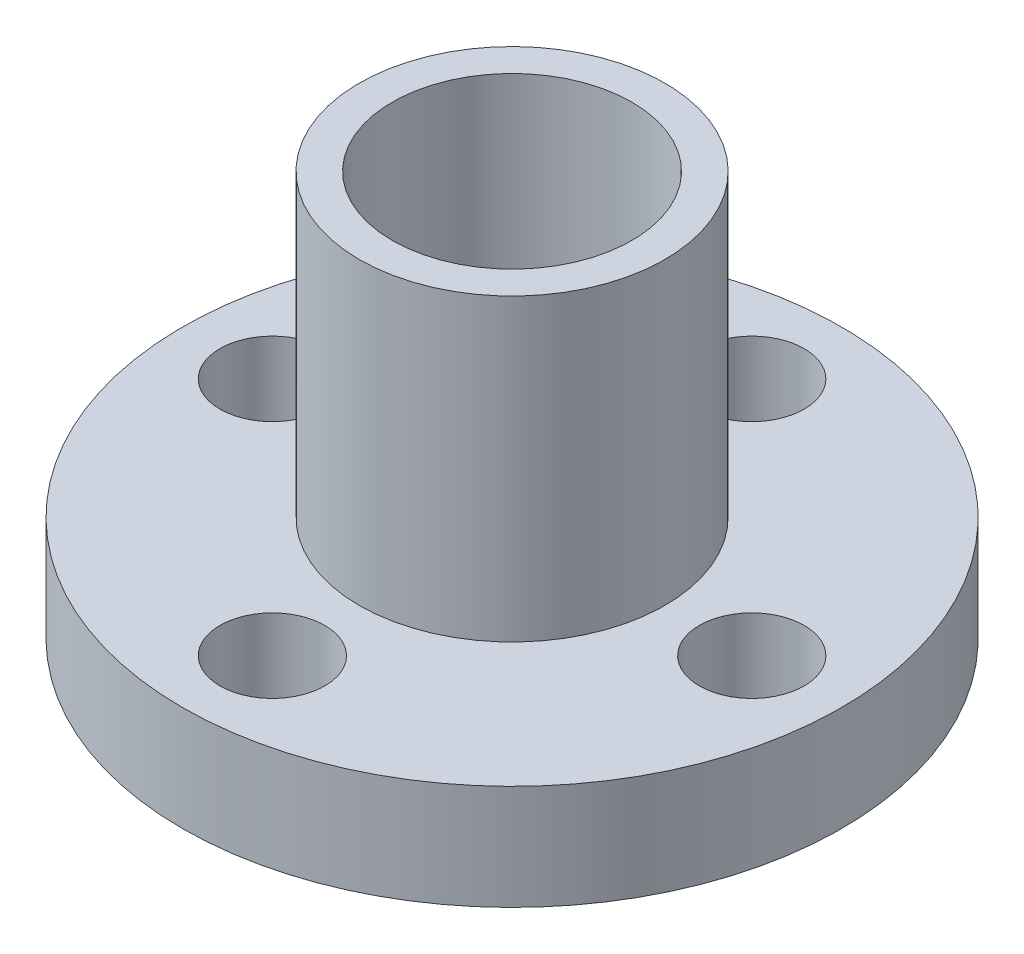
SolidWorks part; units mm, degrees
ref_plane "前视基准面" through (0, 0, 0) normal (0, 0, 1) x (1, 0, 0)
ref_plane "上视基准面" through (0, 0, 0) normal (0, 1, 0) x (1, 0, 0)
ref_plane "右视基准面" through (0, 0, 0) normal (1, 0, 0) x (0, 0, -1)
sketch "草图1" plane through (0, 0, 0) normal (0, 1, 0) x (1, 0, 0)
  circle A0 centre (0, 0) radius 11
sketch "草图2" plane through (0, 0, 0) normal (0, 1, 0) x (1, 0, 0)
  circle A0 centre (0, 0) radius 5.1
extrude "凸台-拉伸2" add sketch "草图2" along normal blind 10 and the other way blind 5
extrude "凸台-拉伸3" add sketch "草图1" against normal blind 3.5 contours A0
sketch "草图3" plane through (0, 0, 0) normal (0, 1, 0) x (1, 0, 0)
  circle A1 centre (-8, 0) radius 1.75
  circle A2 centre (0, 8) radius 1.75
  circle A3 centre (8, 0) radius 1.75
  circle A4 centre (0, -8) radius 1.75
extrude "切除-拉伸1" cut sketch "草图3" against normal blind 5.5
sketch "草图4" plane through (0, 10, 0) normal (0, 1, 0) x (1, 0, 0)
  circle A0 centre (0, 0) radius 4
extrude "切除-拉伸2" cut sketch "草图4" against normal blind 16.5
